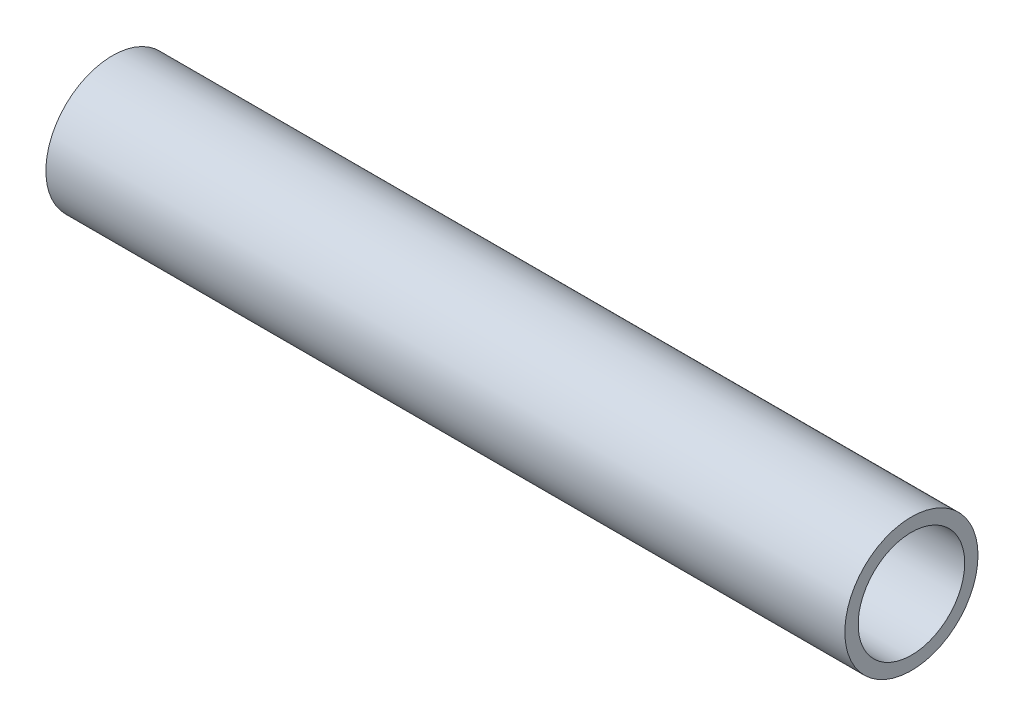
SolidWorks part; units mm, degrees
material "6061-T6 (SS)"
ref_plane "Front Plane" through (0, 0, 0) normal (0, 0, 1) x (1, 0, 0)
ref_plane "Top Plane" through (0, 0, 0) normal (0, 1, 0) x (1, 0, 0)
ref_plane "Right Plane" through (0, 0, 0) normal (1, 0, 0) x (0, 0, -1)
sketch "Sketch1" plane through (0, 0, 0) normal (1, 0, 0) x (0, 0, -1)
  circle A0 centre (0, 0) radius 6.35
  circle A1 centre (0, 0) radius 5.08
  dimension "D1" = 12.7
  dimension "D2" = 1.27
extrude "Boss-Extrude1" add sketch "Sketch1" along normal blind 76.2
